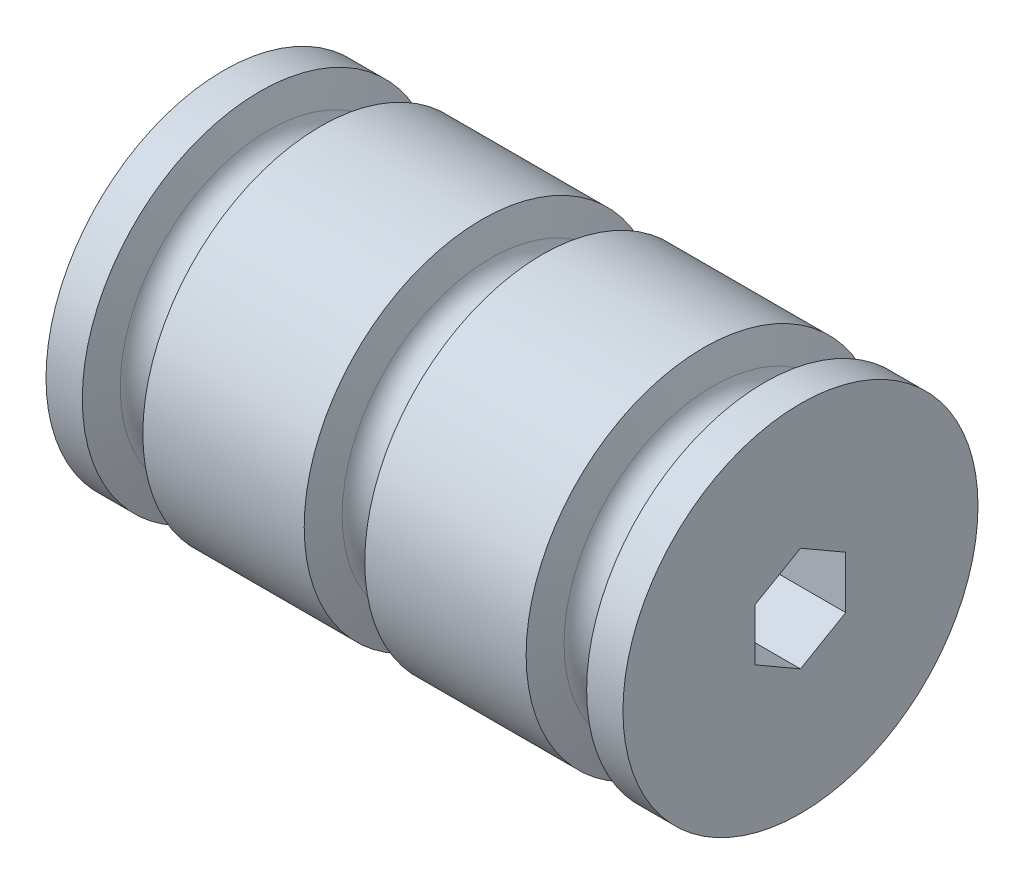
SolidWorks part; units mm, degrees
material "PET"
ref_plane "Front" through (0, 0, 0) normal (0, 0, 1) x (1, 0, 0)
ref_plane "Top" through (0, 0, 0) normal (0, 1, 0) x (1, 0, 0)
ref_plane "Right" through (0, 0, 0) normal (1, 0, 0) x (0, 0, -1)
sketch "Sketch1" plane through (0, 0, 0) normal (0, 0, 1) x (1, 0, 0)
  line L0 (0, 0) -> (-9.1782, 0) construction
  line L1 (0, 0) -> (82.55, 0)
  line L2 (0, 0) -> (0, 25.4)
  line L3 (0, 25.4) -> (82.55, 25.4)
  line L4 (82.55, 0) -> (82.55, 25.4)
  dimension "D1" = 82.55
  dimension "D2" = 50.8
revolve "Revolve1" add sketch "Sketch1" angle 360 about L0
sketch "Sketch2" plane through (0, 0, 0) normal (0, 0, 1) x (1, 0, 0)
  line L0 (5.1948, 25.4) -> (6.4969, 21.2703)
  line L1 (82.55, 25.4) -> (0, 25.4) construction
  line L2 (12.5531, 21.2703) -> (13.8552, 25.4)
  line L3 (13.8552, 25.4) -> (5.1948, 25.4)
  line L4 (36.9448, 25.4) -> (38.2469, 21.2703)
  line L5 (44.3031, 21.2703) -> (45.6052, 25.4)
  line L6 (45.6052, 25.4) -> (36.9448, 25.4)
  line L7 (68.6948, 25.4) -> (69.9969, 21.2703)
  line L8 (76.0531, 21.2703) -> (77.3552, 25.4)
  line L9 (77.3552, 25.4) -> (68.6948, 25.4)
  line L10 (0, 25.4) -> (5.1948, 25.4) construction
  line L11 (77.3552, 25.4) -> (82.55, 25.4) construction
  line L12 (0, 0) -> (-7.0088, 0) construction
  line L13 (0, 25.4) -> (0, -25.4) construction
  arc A0 (6.4969, 21.2703) -> (12.5531, 21.2703) centre (9.525, 22.225) ccw
  arc A1 (38.2469, 21.2703) -> (44.3031, 21.2703) centre (41.275, 22.225) ccw
  arc A2 (69.9969, 21.2703) -> (76.0531, 21.2703) centre (73.025, 22.225) ccw
  dimension "D2" = 3.175
  dimension "D3" = 6.35
  dimension "D1" = 35
  dimension "D5" = 31.75
  dimension "D4" = 3
revolve "Cut-Revolve1" cut sketch "Sketch2" angle 360 about L12
sketch "Sketch3" plane through (0, 0, 0) normal (-1, 0, 0) x (0, 0, 1)
  line L1 (0, 7.479) -> (-6.477, 3.7395)
  line L2 (-6.477, 3.7395) -> (-6.477, -3.7395)
  line L3 (-6.477, -3.7395) -> (0, -7.479)
  line L4 (0, -7.479) -> (6.477, -3.7395)
  line L5 (6.477, -3.7395) -> (6.477, 3.7395)
  line L6 (6.477, 3.7395) -> (0, 7.479)
  circle A0 centre (0, 0) radius 6.477 construction
  dimension "D1" = 12.954
extrude "Cut-Extrude1" cut sketch "Sketch3" against normal through all
